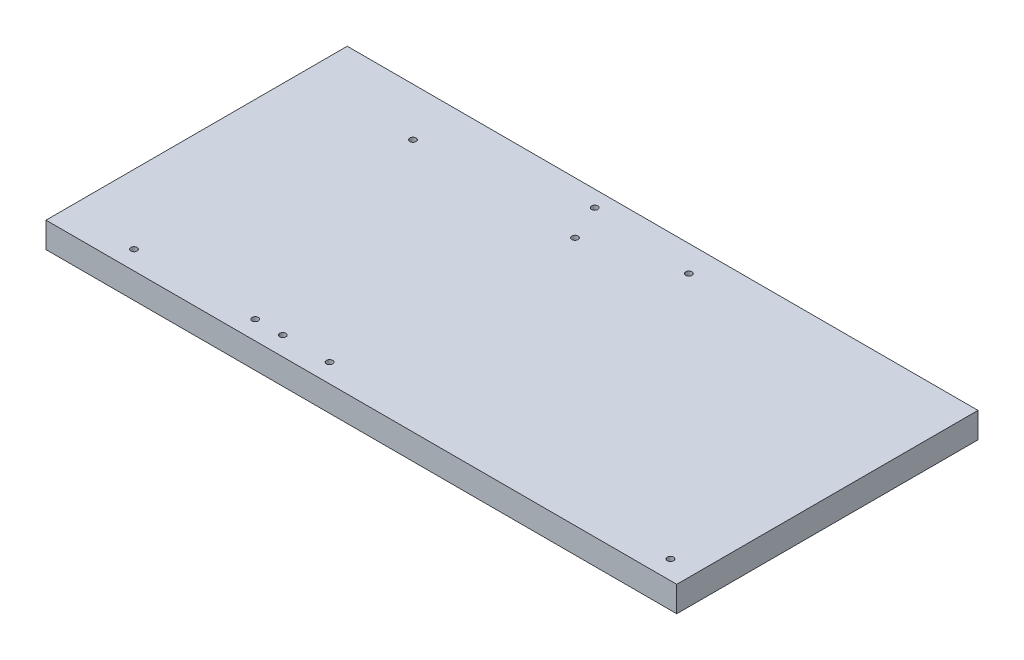
SolidWorks part; units mm, degrees
ref_plane "Front Plane" through (0, 0, 0) normal (0, 0, 1) x (1, 0, 0)
ref_plane "Top Plane" through (0, 0, 0) normal (0, 1, 0) x (1, 0, 0)
ref_plane "Right Plane" through (0, 0, 0) normal (1, 0, 0) x (0, 0, -1)
sketch "Sketch1" plane through (0, 0, 0) normal (0, 1, 0) x (1, 0, 0)
  line L1 (-254.7815, 148.4923) -> (383.3935, 148.4923)
  line L2 (-254.7815, 148.4923) -> (-254.7815, -156.3077)
  line L3 (-254.7815, -156.3077) -> (383.3935, -156.3077)
  line L4 (383.3935, 148.4923) -> (383.3935, -156.3077)
  dimension "D1" = 304.8
  dimension "D2" = 638.175
extrude "Jig stock" add sketch "Sketch1" along normal blind 25.8318
sketch "Sketch3" plane through (0, 25.8318, 0) normal (0, 1, 0) x (1, 0, 0)
  line L0 (-254.7815, -156.3077) -> (383.3935, -156.3077) construction
  line L1 (383.3935, -156.3077) -> (383.3935, 148.4923) construction
  line L2 (-254.7815, -137.2577) -> (383.3935, -137.2577) construction
  line L3 (-254.7815, 148.4923) -> (-254.7815, -156.3077) construction
  line L4 (383.3935, -147.0682) -> (357.9935, -137.2577) construction
  line L5 (357.9935, -137.2577) -> (-9.0686, 148.4923) construction
  line L6 (383.3935, 148.4923) -> (-254.7815, 148.4923) construction
  circle A0 centre (357.9935, -137.2577) radius 3.175
  circle A1 centre (-62.1733, -137.2577) radius 3.175
  circle A2 centre (11.8995, 132.1691) radius 3.175
  dimension "D1" = 6.35
  dimension "D5" = 6.35
  dimension "D6" = 6.35
  dimension "D2" = 19.05
  dimension "D3" = 25.4
  dimension "D4" = 37.9
  dimension "D7" = 438.6021
  dimension "D8" = 420.1668
extrude "Front bottom wishbone" cut sketch "Sketch3" against normal through all
sketch "Sketch5" plane through (0, 25.8318, 0) normal (0, 1, 0) x (1, 0, 0)
  line L0 (383.3935, -137.2577) -> (-254.7815, -137.2577) construction
  line L1 (383.3935, -156.3077) -> (383.3935, 148.4923) construction
  line L2 (-254.7815, 148.4923) -> (-254.7815, -156.3077) construction
  line L3 (357.9935, -137.2577) -> (92.7369, 148.4923) construction
  line L4 (383.3935, 148.4923) -> (-254.7815, 148.4923) construction
  line L5 (-254.7815, -156.3077) -> (383.3935, -156.3077) construction
  circle A0 centre (13.1275, -137.2577) radius 3.175
  circle A1 centre (117.2752, 122.0582) radius 3.175
  dimension "D2" = 6.35
  dimension "D3" = 6.35
  dimension "D1" = 47.13
  dimension "D4" = 353.822
  dimension "D5" = 344.866
extrude "Front top wishbone" cut sketch "Sketch5" against normal through all
sketch "Sketch6" plane through (0, 25.8318, 0) normal (0, 1, 0) x (1, 0, 0)
  line L0 (383.3935, -137.2577) -> (-254.7815, -137.2577) construction
  line L1 (383.3935, -156.3077) -> (383.3935, 148.4923) construction
  line L2 (-254.7815, 148.4923) -> (-254.7815, -156.3077) construction
  line L3 (357.9935, -137.2577) -> (-46.1837, 148.4923) construction
  line L4 (383.3935, 148.4923) -> (-254.7815, 148.4923) construction
  line L5 (-254.7815, -156.3077) -> (383.3935, -156.3077) construction
  circle A0 centre (-34.2537, -137.2577) radius 3.175
  circle A1 centre (28.2792, 95.8476) radius 3.175
  dimension "D1" = 6.35
  dimension "D2" = 6.35
  dimension "D3" = 35.26
  dimension "D4" = 403.794
  dimension "D5" = 392.2471
extrude "Rear top wishbone" cut sketch "Sketch6" against normal through all
sketch "Sketch7" plane through (0, 25.8318, 0) normal (0, 1, 0) x (1, 0, 0)
  line L0 (383.3935, -137.2577) -> (-254.7815, -137.2577) construction
  line L1 (383.3935, -156.3077) -> (383.3935, 148.4923) construction
  line L2 (-254.7815, 148.4923) -> (-254.7815, -156.3077) construction
  line L3 (357.9935, -137.2577) -> (-241.902, 148.4923) construction
  line L4 (383.3935, 148.4923) -> (-254.7815, 148.4923) construction
  line L5 (-254.7815, -156.3077) -> (383.3935, -156.3077) construction
  circle A0 centre (-184.7614, -137.2577) radius 3.175
  circle A1 centre (-139.5993, 99.7622) radius 3.175
  dimension "D2" = 6.35
  dimension "D3" = 6.35
  dimension "D1" = 25.47
  dimension "D4" = 542.7548
  dimension "D5" = 551.1597
extrude "Rear bottom wishbone" cut sketch "Sketch7" against normal through all
